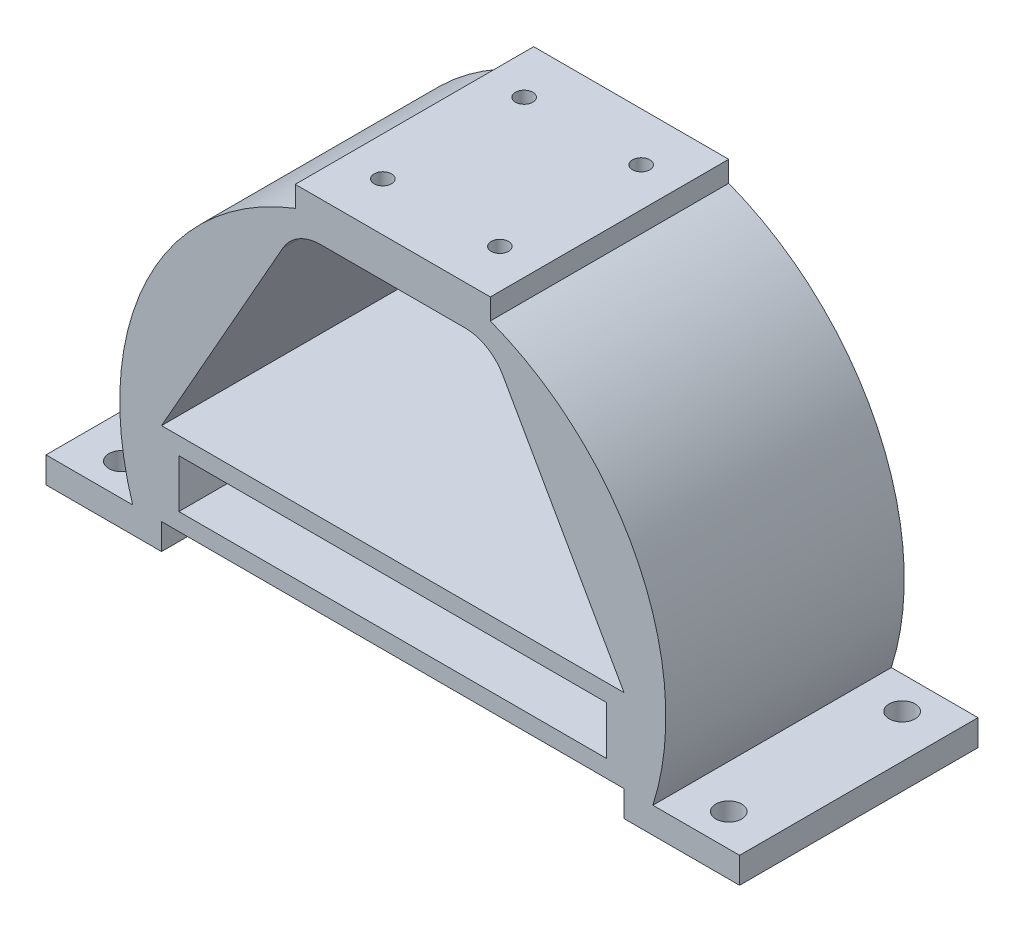
SolidWorks part; units mm, degrees
ref_plane "Front Plane" through (0, 0, 0) normal (0, 0, 1) x (1, 0, 0)
ref_plane "Top Plane" through (0, 0, 0) normal (0, 1, 0) x (1, 0, 0)
ref_plane "Right Plane" through (0, 0, 0) normal (1, 0, 0) x (0, 0, -1)
sketch "Sketch1" plane through (0, 0, 0) normal (0, 0, 1) x (1, 0, 0)
  line L1 (101.6, 0) -> (101.6, 7.62)
  line L2 (101.6, 7.62) -> (76.2, 7.62)
  line L3 (-101.6, 0) -> (-101.6, 7.62)
  line L4 (-101.6, 7.62) -> (-76.2, 7.62)
  line L6 (0, 0) -> (0, 112.776) construction
  line L7 (-28.575, 106.68) -> (-28.575, 112.776)
  line L8 (-28.575, 112.776) -> (28.575, 112.776)
  line L9 (28.575, 112.776) -> (28.575, 106.68)
  line L10 (-101.6, 0) -> (-67.7528, 0)
  line L11 (101.6, 0) -> (67.7528, 0)
  line L12 (-28.575, 101.2139) -> (28.575, 101.2139)
  line L13 (-67.7528, 63.9274) -> (-67.7528, 0)
  line L14 (67.7528, 63.9274) -> (67.7528, 0)
  line L15 (28.575, 101.2139) -> (67.7528, 31.9637)
  line L16 (-28.575, 101.2139) -> (-67.7528, 31.9637)
  arc A0 (-76.2, 7.62) -> (-28.575, 106.68) centre (0, 31.9637) cw
  arc A1 (28.575, 106.68) -> (76.2, 7.62) centre (0, 31.9637) cw
  arc A2 (67.7528, 0) -> (-67.7528, 0) centre (0, 31.9637) ccw
  point P16 (0, 112.776)
  dimension "D3" = 7.62
  dimension "D7" = 5.08
  dimension "D1" = 57.15
  dimension "D2" = 6.096
  dimension "D4" = 25.4
  dimension "D5" = 203.2
  dimension "D6" = 112.776
extrude "Boss-Extrude1" add sketch "Sketch1" along normal blind 69.85 contours A2 L6 L8 L7 A0 L4 L3 L10 | L6 A2 L11 L1 L2 A1 L9 L8 | L14 A2 L15 | L12 L6 A2 | L6 L12 A2 | L16 A2 L13 | L13 A2 | L14 A2
sketch "Sketch2" plane through (0, 0, 69.85) normal (0, 0, 1) x (1, 0, 0)
  line L0 (-67.7528, 31.9637) -> (-67.7528, 0) construction
  line L1 (-67.7528, 31.9637) -> (67.7528, 31.9637)
  line L2 (-67.7528, 31.9637) -> (-67.7528, 7.62)
  line L3 (-67.7528, 7.62) -> (67.7528, 7.62)
  line L4 (67.7528, 31.9637) -> (67.7528, 7.62)
  line L5 (67.7528, 31.9637) -> (67.7528, 0) construction
  line L6 (-101.6, 7.62) -> (-76.2, 7.62) construction
  line L7 (-62.6728, 26.8837) -> (62.6728, 26.8837)
  line L8 (-62.6728, 26.8837) -> (-62.6728, 12.7)
  line L9 (-62.6728, 12.7) -> (62.6728, 12.7)
  line L10 (62.6728, 26.8837) -> (62.6728, 12.7)
  point P19 (-62.6728, 19.7919)
  point P20 (-67.7528, 19.7919)
  point P21 (0, 31.9637)
  point P22 (0, 26.8837)
  dimension "D1" = 5.08
  dimension "D2" = 5.08
extrude "Boss-Extrude2" add sketch "Sketch2" against normal up to surface (69.85 mm away) up to face at (0, 47.1685, 0)
sketch "Sketch3" plane through (0, 0, 0) normal (0, -1, 0) x (-1, 0, 0)
  line L0 (88.9, -69.85) -> (88.9, 0) construction
  line L1 (101.6, -69.85) -> (67.7528, -69.85) construction
  line L2 (101.6, 0) -> (67.7528, 0) construction
  line L3 (-88.9, -69.85) -> (-88.9, 0) construction
  line L4 (-101.6, -69.85) -> (-67.7528, -69.85) construction
  line L5 (-101.6, 0) -> (-67.7528, 0) construction
  line L6 (101.6, -60.325) -> (-101.6, -60.325) construction
  line L7 (101.6, -69.85) -> (101.6, 0) construction
  line L8 (-101.6, -69.85) -> (-101.6, 0) construction
  line L9 (101.6, -9.525) -> (-101.6, -9.525) construction
  line L10 (88.9, -34.925) -> (-88.9, -34.925) construction
  line L11 (0, -60.325) -> (0, -9.525) construction
  circle A0 centre (88.9, -60.325) radius 3.81
  circle A1 centre (88.9, -9.525) radius 3.81
  circle A2 centre (-88.9, -9.525) radius 3.81
  circle A3 centre (-88.9, -60.325) radius 3.81
  point P32 (0, -34.925)
  point P33 (0, -34.925)
  dimension "D1" = 7.62
  dimension "D2" = 50.8
  dimension "D3" = 177.8
extrude "Cut-Extrude1" cut sketch "Sketch3" against normal up to next
sketch "Sketch4" plane through (0, 112.776, 0) normal (0, 1, 0) x (1, 0, 0)
  line L0 (-28.575, -69.85) -> (-28.575, 0) construction
  line L1 (17.145, -55.626) -> (-17.145, -55.626)
  line L2 (17.145, -55.626) -> (17.145, -14.224)
  line L3 (17.145, -14.224) -> (-17.145, -14.224)
  line L4 (-17.145, -55.626) -> (-17.145, -14.224)
  line L5 (17.145, -55.626) -> (-17.145, -14.224) construction
  line L6 (17.145, -14.224) -> (-17.145, -55.626) construction
  circle A0 centre (-17.145, -14.224) radius 2.54
  circle A1 centre (17.145, -14.224) radius 2.54
  circle A2 centre (-17.145, -55.626) radius 2.54
  circle A3 centre (17.145, -55.626) radius 2.54
  point P0 (0, -34.925)
  point P13 (-28.575, -34.925)
  dimension "D1" = 5.08
  dimension "D2" = 41.402
  dimension "D3" = 34.29
extrude "Cut-Extrude2" cut sketch "Sketch4" against normal up to next contours L3 A0 L4 | L2 A1 L3 | L1 A3 L2 | L4 A2 L1 | L1 A2 L4 | L4 A0 L3 | L3 A1 L2 | L2 A3 L1
fillet "Fillet1" radius 12.7 2 edges at (28.575, 101.2139, 34.925) (-28.575, 101.2139, 34.925)
